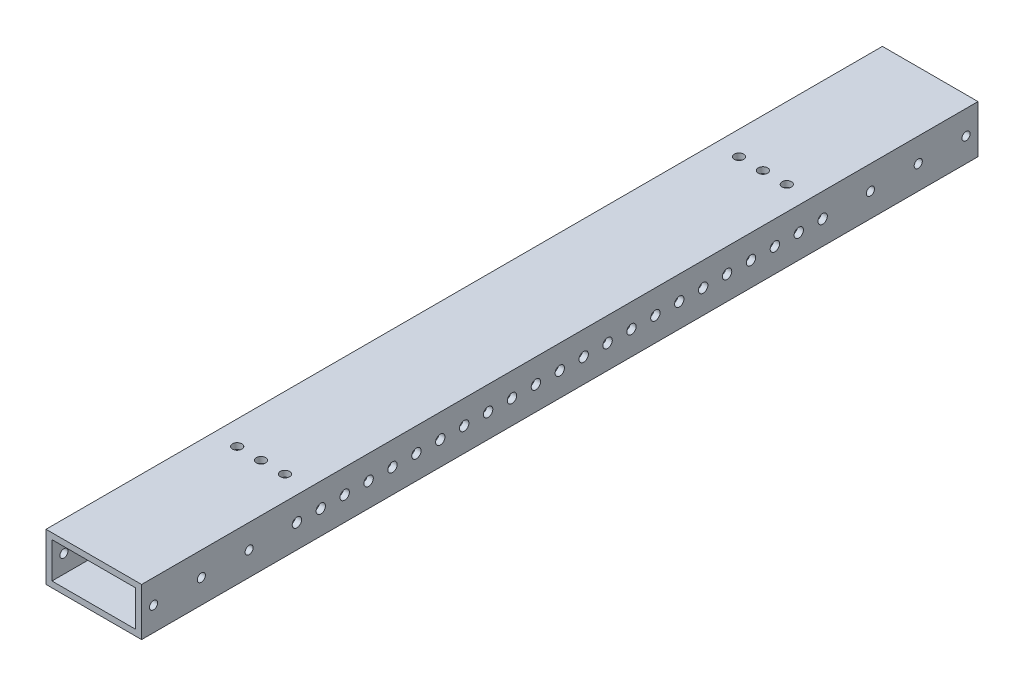
SolidWorks part; units mm, degrees
material "6061-T6 (SS)"
ref_plane "Front Plane" through (0, 0, 0) normal (0, 0, 1) x (1, 0, 0)
ref_plane "Top Plane" through (0, 0, 0) normal (0, 1, 0) x (1, 0, 0)
ref_plane "Right Plane" through (0, 0, 0) normal (1, 0, 0) x (0, 0, -1)
sketch "Sketch1" plane through (0, 0, 0) normal (0, 0, 1) x (1, 0, 0)
  line L0 (-22.225, 9.525) -> (22.225, 9.525)
  line L1 (-25.4, 12.7) -> (25.4, 12.7)
  line L2 (-25.4, 12.7) -> (-25.4, -12.7)
  line L3 (-25.4, -12.7) -> (25.4, -12.7)
  line L4 (25.4, 12.7) -> (25.4, -12.7)
  line L5 (22.225, 9.525) -> (22.225, -9.525)
  line L6 (-22.225, -9.525) -> (22.225, -9.525)
  line L7 (-22.225, 9.525) -> (-22.225, -9.525)
  line L8 (-25.4, 12.7) -> (25.4, -12.7) construction
  line L9 (25.4, 12.7) -> (-25.4, -12.7) construction
  point P5 (0, 0)
  dimension "D1" = 50.8
  dimension "D2" = 25.4
  dimension "D3" = 3.175
extrude "Boss-Extrude1" add sketch "Sketch1" along normal mid plane 444.5
sketch "Sketch3" plane through (25.4, 0, 0) normal (1, 0, 0) x (0, 0, -1)
  line L0 (-222.25, -12.7) -> (-222.25, 12.7) construction
  line L1 (-222.25, 12.7) -> (222.25, 12.7) construction
  line L2 (222.25, -12.7) -> (222.25, 12.7) construction
  circle A0 centre (-215.9, 0) radius 2.1527
  circle A1 centre (-190.5, 0) radius 2.1527
  circle A2 centre (-165.1, 0) radius 2.1527
  circle A3 centre (215.9, 0) radius 2.159
  circle A4 centre (190.5, 0) radius 2.159
  circle A5 centre (165.1, 0) radius 2.159
  dimension "D2" = 4.3053
  dimension "D9" = 4.318
  dimension "D1" = 6.35
  dimension "D3" = 12.7
  dimension "D4" = 31.75
  dimension "D5" = 12.7
  dimension "D6" = 57.15
  dimension "D7" = 12.7
  dimension "D8" = 6.35
  dimension "D10" = 12.7
  dimension "D11" = 31.75
  dimension "D12" = 57.15
  dimension "D13" = 12.7
  dimension "D14" = 12.7
extrude "Cut-Extrude2" cut sketch "Sketch3" against normal through all
sketch "Sketch4" plane through (25.4, 0, 0) normal (1, 0, 0) x (0, 0, -1)
  line L1 (-222.25, -12.7) -> (-222.25, 12.7) construction
  line L2 (-222.25, -12.7) -> (222.25, -12.7) construction
  circle A2 centre (-215.9, 0) radius 2.4892 construction
  circle A3 centre (-203.2, 0) radius 2.4892 construction
  circle A16 centre (-190.5, 0) radius 2.4892 construction
  circle A17 centre (-177.8, 0) radius 2.4892 construction
  circle A18 centre (-165.1, 0) radius 2.4892 construction
  circle A35 centre (-152.4, 0) radius 2.4892
  circle A36 centre (-139.7, 0) radius 2.4892
  circle A37 centre (-127, 0) radius 2.4892
  circle A38 centre (-114.3, 0) radius 2.4892
  circle A39 centre (-101.6, 0) radius 2.4892
  circle A40 centre (-88.9, 0) radius 2.4892
  circle A41 centre (-76.2, 0) radius 2.4892
  circle A42 centre (-63.5, 0) radius 2.4892
  circle A43 centre (-50.8, 0) radius 2.4892
  circle A44 centre (-38.1, 0) radius 2.4892
  circle A45 centre (-25.4, 0) radius 2.4892
  circle A46 centre (-12.7, 0) radius 2.4892
  circle A47 centre (0, 0) radius 2.4892
  circle A48 centre (12.7, 0) radius 2.4892
  circle A49 centre (25.4, 0) radius 2.4892
  circle A50 centre (38.1, 0) radius 2.4892
  circle A51 centre (50.8, 0) radius 2.4892
  circle A52 centre (63.5, 0) radius 2.4892
  circle A53 centre (76.2, 0) radius 2.4892
  circle A54 centre (88.9, 0) radius 2.4892
  circle A55 centre (101.6, 0) radius 2.4892
  circle A56 centre (114.3, 0) radius 2.4892
  circle A57 centre (127, 0) radius 2.4892
  circle A58 centre (139.7, 0) radius 2.4892
  circle A59 centre (152.4, 0) radius 2.4892
  circle A60 centre (165.1, 0) radius 2.4892 construction
  circle A61 centre (177.8, 0) radius 2.4892 construction
  circle A62 centre (190.5, 0) radius 2.4892 construction
  circle A63 centre (203.2, 0) radius 2.4892 construction
  dimension "D2" = 4.9784
  dimension "D1" = 6.35
  dimension "D3" = 12.7
  dimension "D4" = 12.7
  dimension "D5" = 34
extrude "Cut-Extrude3" cut sketch "Sketch4" against normal through all contours A36 | A37 | A38 | A39 | A40 | A41 | A42 | A43 | A44 | A45 | A46 | A47 | A48 | A49 | A50 | A51 | A52 | A53 | A54 | A55 | A56 | A57 | A58
sketch "Sketch5" plane through (0, -12.7, 0) normal (0, -1, 0) x (1, 0, 0)
  line L0 (-25.4, 0) -> (25.4, 0) construction
  line L4 (25.4, 222.25) -> (25.4, -222.25) construction
  line L5 (-25.4, 222.25) -> (-25.4, -222.25) construction
  line L6 (-25.4, 222.25) -> (25.4, 222.25) construction
  circle A0 centre (-12.7, 133.35) radius 2.4892
  circle A1 centre (0, 133.35) radius 2.4892
  circle A2 centre (12.7, 133.35) radius 2.4892
  circle A3 centre (12.7, -133.35) radius 2.4892
  circle A4 centre (0, -133.35) radius 2.4892
  circle A5 centre (-12.7, -133.35) radius 2.4892
  dimension "D1" = 4.9784
  dimension "D3" = 12.7
  dimension "D2" = 88.9
  dimension "D5" = 12.7
  dimension "D4" = 12.7
extrude "Cut-Extrude4" cut sketch "Sketch5" against normal through all
